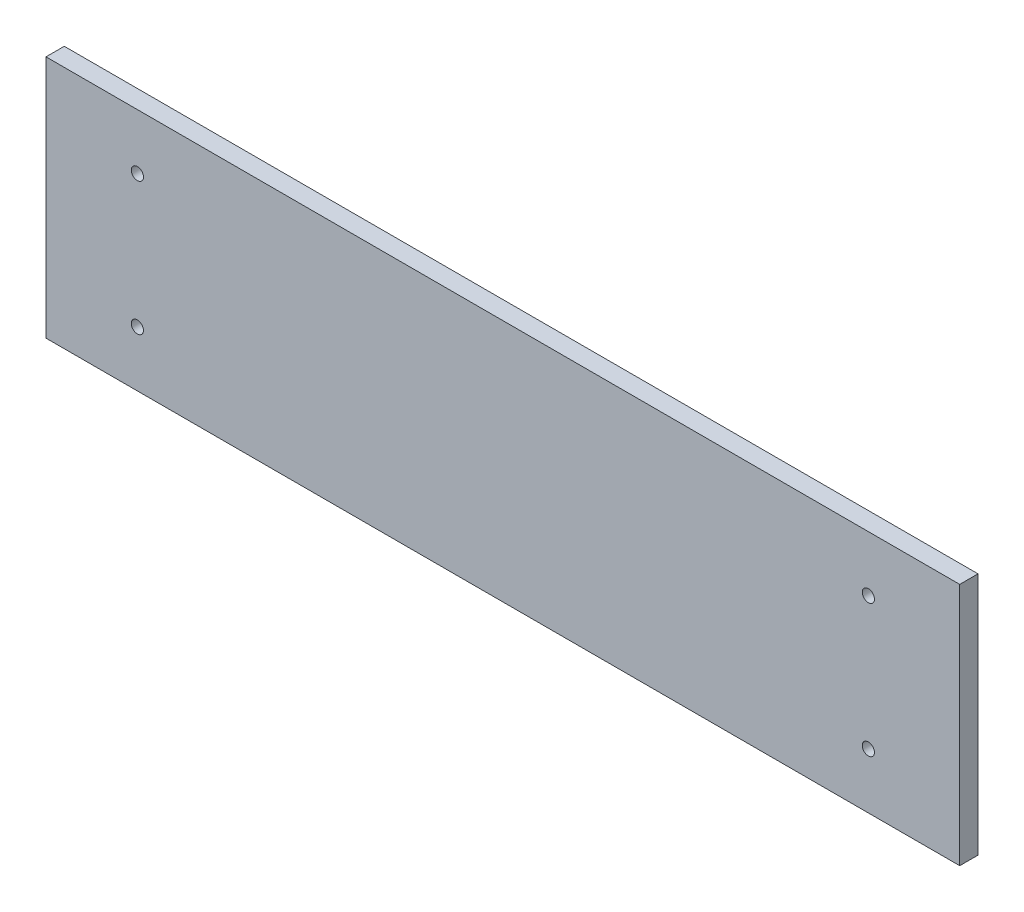
SolidWorks part; units mm, degrees
ref_plane "Front Plane" through (0, 0, 0) normal (0, 0, 1) x (1, 0, 0)
ref_plane "Top Plane" through (0, 0, 0) normal (0, 1, 0) x (1, 0, 0)
ref_plane "Right Plane" through (0, 0, 0) normal (1, 0, 0) x (0, 0, -1)
sketch "Sketch1" plane through (0, 0, 0) normal (0, 0, 1) x (1, 0, 0)
  line L1 (-77.4869, -14.2147) -> (72.5131, -14.2147)
  line L2 (-77.4869, -14.2147) -> (-77.4869, 25.7853)
  line L3 (-77.4869, 25.7853) -> (72.5131, 25.7853)
  line L4 (72.5131, -14.2147) -> (72.5131, 25.7853)
  dimension "D1" = 150
  dimension "D2" = 40
extrude "Boss-Extrude1" add sketch "Sketch1" along normal blind 3
sketch "Sketch2" plane through (0, 0, 3) normal (0, 0, 1) x (1, 0, 0)
  line L3 (-77.4869, 25.7853) -> (-77.4869, -14.2147) construction
  line L5 (72.5131, -14.2147) -> (72.5131, 25.7853) construction
  line L6 (-77.4869, 5.7853) -> (72.5131, 5.7853) construction
  circle A0 centre (-62.4869, 16.6853) radius 1
  circle A2 centre (57.5131, 16.6853) radius 1
  circle A4 centre (57.5131, -5.1147) radius 1
  circle A5 centre (-62.4869, -5.1147) radius 1
  dimension "D3" = 2
  dimension "D5" = 2
  dimension "D1" = 10.9
  dimension "D8" = 10.9
extrude "Cut-Extrude1" cut sketch "Sketch2" against normal blind 10
